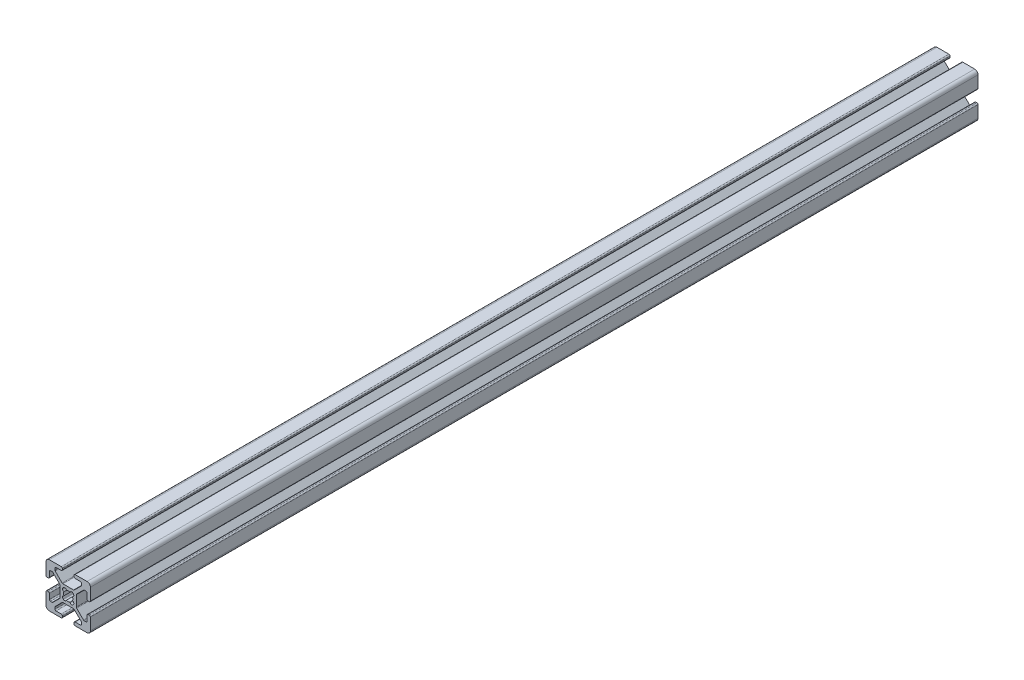
SolidWorks part; units mm, degrees
material "6063-O, Barre extrudée (SS)"
ref_plane "Front Plane" through (0, 0, 0) normal (0, 0, 1) x (1, 0, 0)
ref_plane "Top Plane" through (0, 0, 0) normal (0, 1, 0) x (1, 0, 0)
ref_plane "Right Plane" through (0, 0, 0) normal (1, 0, 0) x (0, 0, -1)
sketch "Sketch1" plane through (0, 0, 0) normal (0, 0, 1) x (1, 0, 0)
  line L0 (-5.0323, -0.3411) -> (-5.5163, -0.3411)
  line L1 (-6.0243, 0.1669) -> (-6.0243, 2.5159)
  line L2 (-4.5243, 0.1669) -> (-4.5243, 5.5289)
  line L3 (-10.8693, -5.355) -> (-10.8693, -0.5871)
  line L4 (-7.2582, 3.0239) -> (-6.5323, 3.0239)
  line L5 (-7.6174, 2.8752) -> (-10.7205, -0.2279)
  line L6 (-5.0323, -5.6011) -> (-5.5163, -5.6011)
  line L7 (-4.5243, -6.1091) -> (-4.5243, -11.4711)
  line L8 (-6.0243, -6.1091) -> (-6.0243, -8.4581)
  line L9 (-7.2582, -8.9661) -> (-6.5323, -8.9661)
  line L10 (-7.6174, -8.8173) -> (-10.7205, -5.7142)
  line L11 (-12.3994, -5.2756) -> (-12.2198, -5.096)
  line L12 (-17.1543, 6.5209) -> (-17.1543, 6.0369)
  line L13 (-17.6623, 7.0289) -> (-23.0243, 7.0289)
  line L14 (-17.6623, 5.5289) -> (-20.0113, 5.5289)
  line L15 (-12.1404, 0.6839) -> (-16.9082, 0.6839)
  line L16 (-20.5193, 4.295) -> (-20.5193, 5.0209)
  line L17 (-20.3705, 3.9358) -> (-17.2674, 0.8327)
  line L18 (-11.8943, 6.5209) -> (-11.8943, 6.0369)
  line L19 (-11.3863, 7.0289) -> (-6.0243, 7.0289)
  line L20 (-11.3863, 5.5289) -> (-9.0373, 5.5289)
  line L21 (-8.5293, 4.295) -> (-8.5293, 5.0209)
  line L22 (-8.6781, 3.9358) -> (-11.7812, 0.8327)
  line L23 (-12.2198, -0.8462) -> (-12.3994, -0.6666)
  line L24 (-24.0163, -5.6011) -> (-23.5323, -5.6011)
  line L25 (-24.5243, -6.1091) -> (-24.5243, -11.4711)
  line L26 (-23.0243, -6.1091) -> (-23.0243, -8.4581)
  line L27 (-18.1793, -0.5871) -> (-18.1793, -5.355)
  line L28 (-21.7904, -8.9661) -> (-22.5163, -8.9661)
  line L29 (-21.4312, -8.8173) -> (-18.3281, -5.7142)
  line L30 (-24.0163, -0.3411) -> (-23.5323, -0.3411)
  line L31 (-24.5243, 0.1669) -> (-24.5243, 5.5289)
  line L32 (-23.0243, 0.1669) -> (-23.0243, 2.5159)
  line L33 (-21.7904, 3.0239) -> (-22.5163, 3.0239)
  line L34 (-21.4312, 2.8752) -> (-18.3281, -0.2279)
  line L35 (-16.6492, -0.6666) -> (-16.8288, -0.8462)
  line L36 (-11.8943, -12.4631) -> (-11.8943, -11.9791)
  line L37 (-11.3863, -12.9711) -> (-6.0243, -12.9711)
  line L38 (-11.3863, -11.4711) -> (-9.0373, -11.4711)
  line L39 (-16.9082, -6.6261) -> (-12.1404, -6.6261)
  line L40 (-8.5293, -10.2371) -> (-8.5293, -10.9631)
  line L41 (-8.6781, -9.8779) -> (-11.7812, -6.7748)
  line L42 (-17.1543, -12.4631) -> (-17.1543, -11.9791)
  line L43 (-17.6623, -12.9711) -> (-23.0243, -12.9711)
  line L44 (-17.6623, -11.4711) -> (-20.0113, -11.4711)
  line L45 (-20.5193, -10.2371) -> (-20.5193, -10.9631)
  line L46 (-20.3705, -9.8779) -> (-17.2674, -6.7748)
  line L47 (-16.8288, -5.096) -> (-16.6492, -5.2756)
  arc A0 (-15.3283, -4.9062) -> (-13.7203, -4.9062) centre (-14.5243, -2.9711) ccw
  arc A1 (-6.0243, 2.5159) -> (-6.5323, 3.0239) centre (-6.5323, 2.5159) ccw
  arc A2 (-7.2582, 3.0239) -> (-7.6174, 2.8752) centre (-7.2582, 2.5159) ccw
  arc A3 (-10.7205, -0.2279) -> (-10.8693, -0.5871) centre (-10.3613, -0.5871) ccw
  arc A4 (-10.8693, -5.355) -> (-10.7205, -5.7142) centre (-10.3613, -5.355) ccw
  arc A5 (-7.6174, -8.8173) -> (-7.2582, -8.9661) centre (-7.2582, -8.4581) ccw
  arc A6 (-6.5323, -8.9661) -> (-6.0243, -8.4581) centre (-6.5323, -8.4581) ccw
  arc A7 (-5.5163, -5.6011) -> (-6.0243, -6.1091) centre (-5.5163, -6.1091) ccw
  arc A8 (-4.5243, -6.1091) -> (-5.0323, -5.6011) centre (-5.0323, -6.1091) ccw
  arc A9 (-5.0323, -0.3411) -> (-4.5243, 0.1669) centre (-5.0323, 0.1669) ccw
  arc A10 (-6.0243, 0.1669) -> (-5.5163, -0.3411) centre (-5.5163, 0.1669) ccw
  arc A11 (-13.7203, -4.9062) -> (-12.3994, -5.2756) centre (-12.9559, -4.7191) ccw
  arc A12 (-12.2198, -5.096) -> (-12.5892, -3.775) centre (-12.7763, -4.5395) ccw
  arc A13 (-17.1543, 6.5209) -> (-17.6623, 7.0289) centre (-17.6623, 6.5209) ccw
  arc A14 (-17.6623, 5.5289) -> (-17.1543, 6.0369) centre (-17.6623, 6.0369) ccw
  arc A15 (-12.5892, -3.775) -> (-12.5892, -2.1671) centre (-14.5243, -2.9711) ccw
  arc A16 (-17.2674, 0.8327) -> (-16.9082, 0.6839) centre (-16.9082, 1.1919) ccw
  arc A17 (-20.0113, 5.5289) -> (-20.5193, 5.0209) centre (-20.0113, 5.0209) ccw
  arc A18 (-20.5193, 4.295) -> (-20.3705, 3.9358) centre (-20.0113, 4.295) ccw
  arc A19 (-11.8943, 6.0369) -> (-11.3863, 5.5289) centre (-11.3863, 6.0369) ccw
  arc A20 (-11.3863, 7.0289) -> (-11.8943, 6.5209) centre (-11.3863, 6.5209) ccw
  arc A21 (-8.5293, 5.0209) -> (-9.0373, 5.5289) centre (-9.0373, 5.0209) ccw
  arc A22 (-8.6781, 3.9358) -> (-8.5293, 4.295) centre (-9.0373, 4.295) ccw
  arc A23 (-12.1404, 0.6839) -> (-11.7812, 0.8327) centre (-12.1404, 1.1919) ccw
  arc A24 (-12.5892, -2.1671) -> (-12.2198, -0.8462) centre (-12.7763, -1.4027) ccw
  arc A25 (-12.3994, -0.6666) -> (-13.7203, -1.0359) centre (-12.9559, -1.223) ccw
  arc A26 (-24.0163, -5.6011) -> (-24.5243, -6.1091) centre (-24.0163, -6.1091) ccw
  arc A27 (-23.0243, -6.1091) -> (-23.5323, -5.6011) centre (-23.5323, -6.1091) ccw
  arc A28 (-13.7203, -1.0359) -> (-15.3283, -1.0359) centre (-14.5243, -2.9711) ccw
  arc A29 (-18.3281, -5.7142) -> (-18.1793, -5.355) centre (-18.6873, -5.355) ccw
  arc A30 (-23.0243, -8.4581) -> (-22.5163, -8.9661) centre (-22.5163, -8.4581) ccw
  arc A31 (-21.7904, -8.9661) -> (-21.4312, -8.8173) centre (-21.7904, -8.4581) ccw
  arc A32 (-23.5323, -0.3411) -> (-23.0243, 0.1669) centre (-23.5323, 0.1669) ccw
  arc A33 (-24.5243, 0.1669) -> (-24.0163, -0.3411) centre (-24.0163, 0.1669) ccw
  arc A34 (-22.5163, 3.0239) -> (-23.0243, 2.5159) centre (-22.5163, 2.5159) ccw
  arc A35 (-21.4312, 2.8752) -> (-21.7904, 3.0239) centre (-21.7904, 2.5159) ccw
  arc A36 (-18.1793, -0.5871) -> (-18.3281, -0.2279) centre (-18.6873, -0.5871) ccw
  arc A37 (-15.3283, -1.0359) -> (-16.6492, -0.6666) centre (-16.0927, -1.223) ccw
  arc A38 (-16.8288, -0.8462) -> (-16.4594, -2.1671) centre (-16.2723, -1.4027) ccw
  arc A39 (-11.8943, -12.4631) -> (-11.3863, -12.9711) centre (-11.3863, -12.4631) ccw
  arc A40 (-11.3863, -11.4711) -> (-11.8943, -11.9791) centre (-11.3863, -11.9791) ccw
  arc A41 (-16.4594, -2.1671) -> (-16.4594, -3.775) centre (-14.5243, -2.9711) ccw
  arc A42 (-11.7812, -6.7748) -> (-12.1404, -6.6261) centre (-12.1404, -7.1341) ccw
  arc A43 (-9.0373, -11.4711) -> (-8.5293, -10.9631) centre (-9.0373, -10.9631) ccw
  arc A44 (-8.5293, -10.2371) -> (-8.6781, -9.8779) centre (-9.0373, -10.2371) ccw
  arc A45 (-17.1543, -11.9791) -> (-17.6623, -11.4711) centre (-17.6623, -11.9791) ccw
  arc A46 (-17.6623, -12.9711) -> (-17.1543, -12.4631) centre (-17.6623, -12.4631) ccw
  arc A47 (-20.5193, -10.9631) -> (-20.0113, -11.4711) centre (-20.0113, -10.9631) ccw
  arc A48 (-20.3705, -9.8779) -> (-20.5193, -10.2371) centre (-20.0113, -10.2371) ccw
  arc A49 (-16.9082, -6.6261) -> (-17.2674, -6.7748) centre (-16.9082, -7.1341) ccw
  arc A50 (-16.4594, -3.775) -> (-16.8288, -5.096) centre (-16.2723, -4.5395) ccw
  arc A51 (-16.6492, -5.2756) -> (-15.3283, -4.9062) centre (-16.0927, -4.7191) ccw
  arc A52 (-4.5243, 5.5289) -> (-6.0243, 7.0289) centre (-6.0243, 5.5289) ccw
  arc A53 (-6.0243, -12.9711) -> (-4.5243, -11.4711) centre (-6.0243, -11.4711) ccw
  arc A54 (-24.5243, -11.4711) -> (-23.0243, -12.9711) centre (-23.0243, -11.4711) ccw
  arc A55 (-23.0243, 7.0289) -> (-24.5243, 5.5289) centre (-23.0243, 5.5289) ccw
extrude "Extrude1" add sketch "Sketch1" along normal blind 400
move or copy body "Corps-Déplacer/Copier1" [suppressed] bodies to move or copy 102
